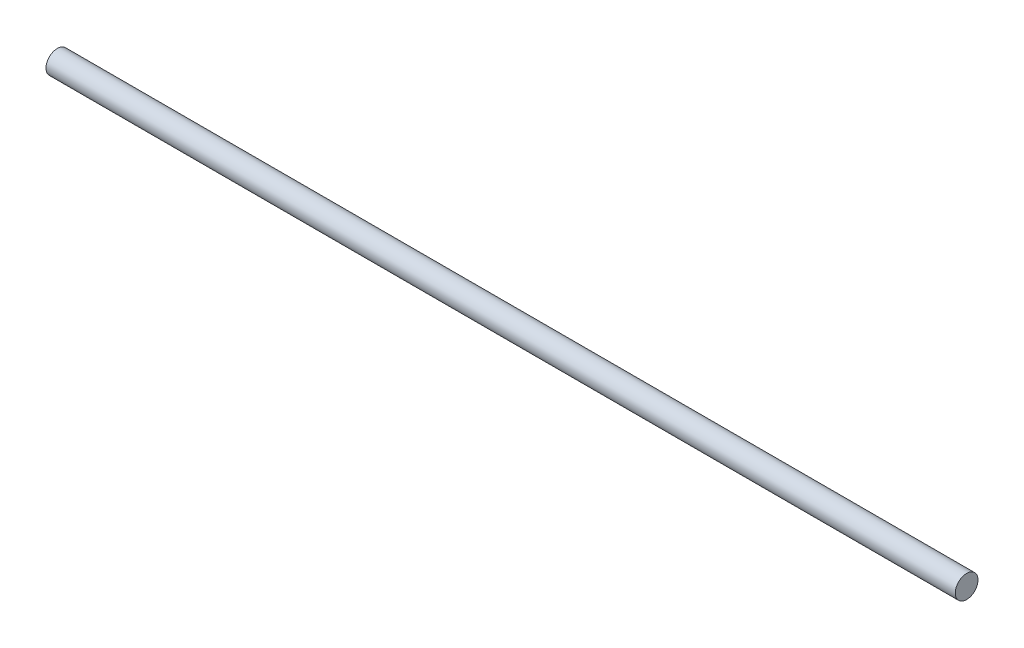
SolidWorks part; units mm, degrees
ref_plane "Front Plane" through (0, 0, 0) normal (0, 0, 1) x (1, 0, 0)
ref_plane "Top Plane" through (0, 0, 0) normal (0, 1, 0) x (1, 0, 0)
ref_plane "Right Plane" through (0, 0, 0) normal (1, 0, 0) x (0, 0, -1)
sketch "Sketch1" plane through (0, 0, 0) normal (0, 0, 1) x (1, 0, 0)
  line L0 (-45.9797, 5.4791) -> (74.0203, 5.4791)
  line L1 (74.0203, 5.4791) -> (74.0203, 3.9791)
  line L2 (74.0203, 3.9791) -> (-45.9797, 3.9791)
  line L3 (-45.9797, 3.9791) -> (-45.9797, 5.4791)
  dimension "D1" = 1.5
  dimension "D2" = 120
revolve "Revolve1" add sketch "Sketch1" angle 360 about L2
